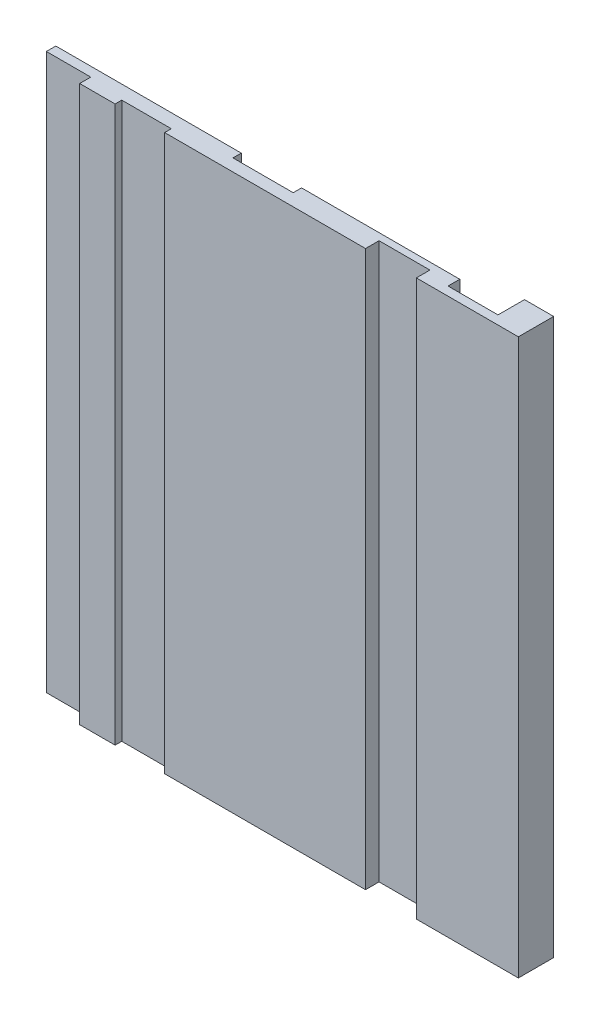
SolidWorks part; units mm, degrees
material "6061 Alloy"
ref_plane "Front Plane" through (0, 0, 0) normal (0, 0, 1) x (1, 0, 0)
ref_plane "Top Plane" through (0, 0, 0) normal (0, 1, 0) x (1, 0, 0)
ref_plane "Right Plane" through (0, 0, 0) normal (1, 0, 0) x (0, 0, -1)
sketch "Sketch1" plane through (0, 0, 0) normal (0, 1, 0) x (1, 0, 0)
  line L0 (-87, 3.7) -> (-53.6, 3.7)
  line L1 (0, 0) -> (-18.37, 0)
  line L2 (0, 0) -> (0, 6.35)
  line L3 (0, 6.35) -> (-5.25, 6.35)
  line L4 (-87, 2) -> (-87, 3.7)
  line L5 (-5.25, 3.7) -> (-5.25, 6.35)
  line L6 (-14.25, 3.7) -> (-14.25, 1.58)
  line L7 (-14.25, 1.58) -> (-5.25, 1.58)
  line L8 (-5.25, 1.58) -> (-5.25, 3.7)
  line L9 (-18.37, 0) -> (-18.37, 2.44)
  line L10 (-18.37, 2.44) -> (-27.53, 2.44)
  line L11 (-27.53, 2.44) -> (-27.53, 0)
  line L12 (-42.75, 3.7) -> (-42.75, 2.2)
  line L13 (-42.75, 2.2) -> (-53.6, 2.2)
  line L14 (-53.6, 2.2) -> (-53.6, 3.7)
  line L15 (-87, 2) -> (-79, 2)
  line L16 (-79, 2) -> (-79, 0)
  line L17 (-72.62, 0) -> (-72.62, 1.2)
  line L18 (-72.62, 1.2) -> (-63.7, 1.2)
  line L19 (-63.7, 1.2) -> (-63.7, 0)
  line L20 (-72.62, 0) -> (-79, 0)
  line L21 (-42.75, 3.7) -> (-14.25, 3.7)
  line L22 (-27.53, 0) -> (-63.7, 0)
  dimension "D1" = 3.7
  dimension "D2" = 6.35
  dimension "D3" = 87
  dimension "D4" = 5.25
  dimension "D5" = 9
  dimension "D6" = 18.37
  dimension "D7" = 9.16
  dimension "D8" = 42.75
  dimension "D9" = 10.85
  dimension "D10" = 8.92
  dimension "D11" = 2.12
  dimension "D12" = 1.5
  dimension "D13" = 2.44
  dimension "D14" = 1.2
  dimension "D15" = 2
  dimension "D16" = 79
  dimension "D17" = 63.7
extrude "Boss-Extrude1" add sketch "Sketch1" along normal blind 100
